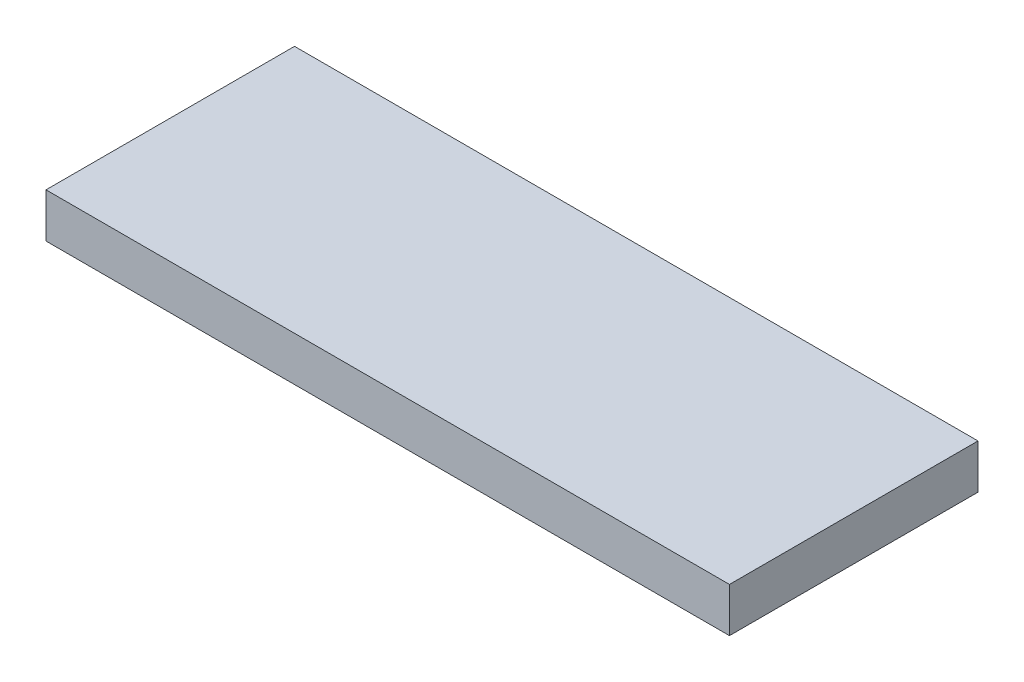
SolidWorks part; units mm, degrees
ref_plane "Front Plane" through (0, 0, 0) normal (0, 0, 1) x (1, 0, 0)
ref_plane "Top Plane" through (0, 0, 0) normal (0, 1, 0) x (1, 0, 0)
ref_plane "Right Plane" through (0, 0, 0) normal (1, 0, 0) x (0, 0, -1)
sketch "Sketch1" plane through (0, 0, 0) normal (0, 1, 0) x (1, 0, 0)
  line L1 (77, 28) -> (-77, 28)
  line L2 (77, 28) -> (77, -28)
  line L3 (77, -28) -> (-77, -28)
  line L4 (-77, 28) -> (-77, -28)
  line L5 (77, 28) -> (-77, -28) construction
  line L6 (77, -28) -> (-77, 28) construction
  point P0 (0, 0)
  dimension "D1" = 154
  dimension "D2" = 56
extrude "base" add sketch "Sketch1" along normal blind 10 contours L1 L4 L3 L2
sketch "Sketch2" plane through (0, 0, 0) normal (0, -1, 0) x (1, 0, 0)
  circle A0 centre (0, 0) radius 3
  dimension "D1" = 6
extrude "load cell button cut" [suppressed] cut sketch "Sketch2" against normal blind 2
sketch "Sketch4" plane through (0, 0, 0) normal (1, 0, 0) x (0, 0, -1)
  line L0 (3, 0) -> (3, 2)
  line L1 (3, 2) -> (0, 3.7321)
  line L2 (0, 3.7321) -> (0, 0) construction
  line L3 (0, 0) -> (3, 0)
  line L4 (0, 3.7321) -> (0, 0)
  point P2 (0, 0)
  point P6 (0, -0.5522)
  point P7 (1.6467, 1.0826)
  point P8 (0, 0)
  point P10 (0, 4.6816)
  dimension "D1" = 3
  dimension "D2" = 2
  dimension "D3" = 60
revolve "Cut-Revolve1" cut sketch "Sketch4" angle 360 about L2
equation "\"D2@Sketch1\"=46+10"
equation "\"D1@Sketch1\"=144+10"
